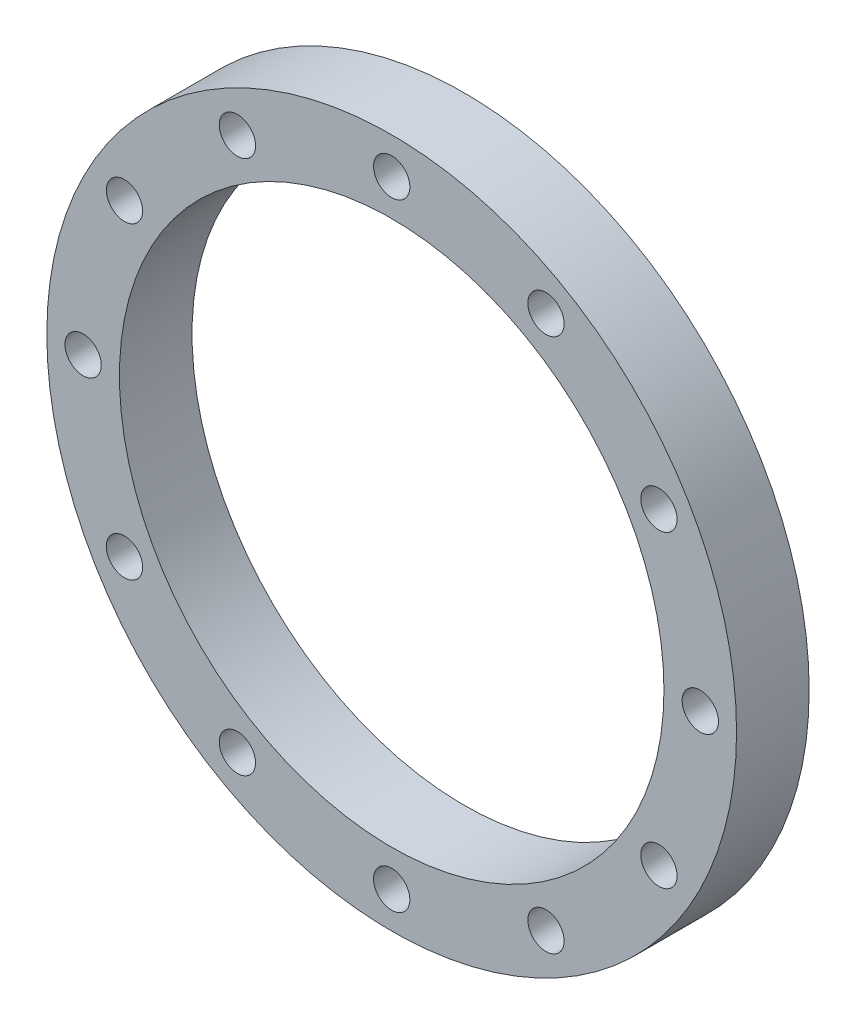
SolidWorks part; units mm, degrees
ref_plane "Front Plane" through (0, 0, 0) normal (0, 0, 1) x (1, 0, 0)
ref_plane "Top Plane" through (0, 0, 0) normal (0, 1, 0) x (1, 0, 0)
ref_plane "Right Plane" through (0, 0, 0) normal (1, 0, 0) x (0, 0, -1)
sketch "Sketch1" plane through (0, 0, 0) normal (0, 0, 1) x (1, 0, 0)
  circle A0 centre (0, 0) radius 190.5
  circle A1 centre (0, 0) radius 241.3
  dimension "D1" = 381
  dimension "D2" = 482.6
extrude "Boss-Extrude1" add sketch "Sketch1" along normal mid plane 50.8
sketch "Sketch2" plane through (0, 0, 0) normal (0, 0, 1) x (1, 0, 0)
  circle A0 centre (0, 0) radius 241.3 construction
  circle A1 centre (0, 0) radius 190.5 construction
  circle A2 centre (0, 0) radius 241.3 construction
  circle A3 centre (0, 0) radius 190.5 construction
  circle A4 centre (0, 0) radius 215.9 construction
  circle A5 centre (215.9, 0) radius 12.7 construction
  dimension "D1" = 431.8
  dimension "D2" = 25.4
hole_wizard "1 (1) Diameter Hole1" positions "Sketch3" profile "Sketch4" hole size "1" standard "ANSI Inch" end condition through all
sketch "Sketch3" plane through (0, 0, 25.4) normal (0, 0, 1) x (1, 0, 0)
  point P0 (215.9, 0)
  point P5 (215.9, 0)
sketch "Sketch4" plane through (215.9, 0, 25.4) normal (1, 0, 0) x (0, -1, 0)
  line L0 (0, 0) -> (0, 50.8)
  line L1 (0, 50.8) -> (12.7, 50.8)
  line L2 (12.7, 50.8) -> (12.7, 0)
  line L5 (12.7, 0) -> (0, 0)
  line L11 (0, -6.35) -> (0, 107.95) construction
  dimension "Thru Hole Dia." = 25.4
  dimension "Thru Hole Depth" = 50.8
pattern_circular "CirPattern1" count 12 over 360 about axis through (0, 0, 0) along (0, 0, 1) of "1 (1) Diameter Hole1"
